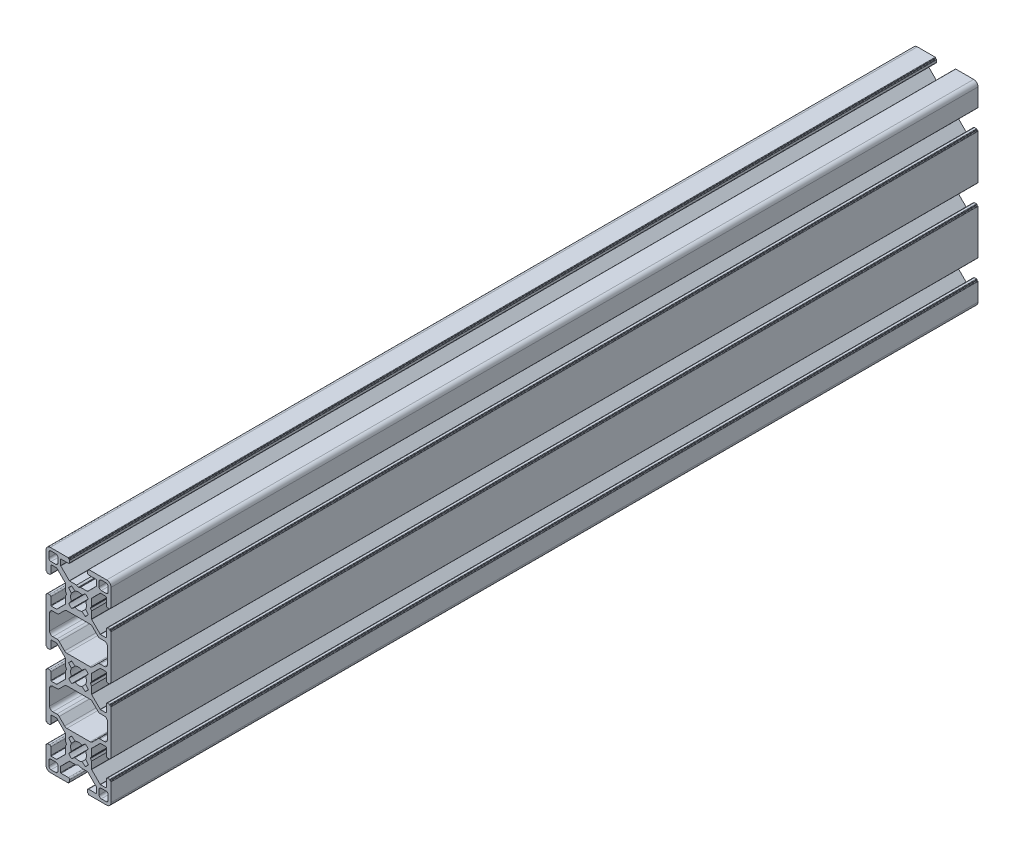
SolidWorks part; units mm, degrees
ref_plane "Спереди" through (0, 0, 0) normal (0, 0, 1) x (1, 0, 0)
ref_plane "Сверху" through (0, 0, 0) normal (0, 1, 0) x (1, 0, 0)
ref_plane "Справа" through (0, 0, 0) normal (1, 0, 0) x (0, 0, -1)
sketch "Эскиз1" plane through (0, 0, 0) normal (0, 0, 1) x (1, 0, 0)
  line L1 (6.0045, 46.509) -> (5.5426, 45.709)
  line L2 (1.6001, 12.3284) -> (3.1547, 11.1036)
  line L3 (4.1172, 9.609) -> (0.9, 9.609)
  line L4 (4.35, 1.109) -> (4.25, 1.109)
  line L5 (4.05, 1.309) -> (4.05, 2.209)
  line L6 (4.55, 0.909) -> (4.55, 0.809)
  line L7 (0.9, 9.609) -> (0.1019, 10.0697)
  line L8 (1.6001, 18.8895) -> (3.1547, 20.1143)
  line L9 (3.2806, 17.2091) -> (4.5184, 18.7449)
  line L10 (3.2806, 14.0088) -> (4.5184, 12.473)
  line L11 (6.0045, 11.4873) -> (6.0045, 14.709)
  line L12 (12.6, 7.359) -> (10.1328, 7.359)
  line L13 (10.5, 6.109) -> (12.7, 6.109)
  line L14 (12.7, 1.909) -> (10.5, 1.909)
  line L15 (15, 2.609) -> (15, 10.859)
  line L16 (13.7, 5.109) -> (13.7, 2.909)
  line L17 (14.8, 11.059) -> (14.7, 11.059)
  line L18 (14.5, 11.259) -> (14.5, 11.359)
  line L19 (14.3, 11.559) -> (13.4, 11.559)
  line L20 (12.8, 10.959) -> (12.8, 7.559)
  line L21 (8.25, 3.009) -> (8.25, 5.4761)
  line L22 (9.5, 2.909) -> (9.5, 5.109)
  line L23 (9.9914, 7.4175) -> (6.063, 11.3459)
  line L24 (12.8, 20.259) -> (12.8, 23.659)
  line L25 (15, 40.859) -> (15, 20.359)
  line L26 (9.9914, 23.8004) -> (6.063, 19.872)
  line L27 (8.9272, 25.0696) -> (6.4104, 22.5528)
  line L28 (14.3, 19.659) -> (13.4, 19.659)
  line L29 (14.5, 19.959) -> (14.5, 19.859)
  line L30 (14.8, 20.159) -> (14.7, 20.159)
  line L31 (6.0045, 19.7306) -> (6.0045, 16.509)
  line L32 (6.0045, 14.709) -> (5.5426, 15.509)
  line L33 (6.0045, 16.509) -> (5.5426, 15.709)
  line L34 (12.6, 23.859) -> (10.1328, 23.859)
  line L35 (11.85, 25.509) -> (9.9879, 25.509)
  line L36 (13.35, 34.209) -> (13.35, 27.009)
  line L37 (4.75, 0.609) -> (13, 0.609)
  line L38 (8.1914, 5.6175) -> (4.2586, 9.5504)
  line L39 (4.65, 2.809) -> (8.05, 2.809)
  line L46 (-1.6001, 42.3284) -> (-3.1547, 41.1036)
  line L47 (-5.3497, 39.1045) -> (5.3497, 39.1045)
  line L48 (-3.2806, 44.0088) -> (-4.5184, 42.473)
  line L63 (-12.8, 40.959) -> (-12.8, 37.559)
  line L64 (-9.9914, 37.4175) -> (-6.063, 41.3459)
  line L65 (-8.9272, 36.1483) -> (-6.4104, 38.6652)
  line L66 (-14.3, 41.559) -> (-13.4, 41.559)
  line L67 (-14.5, 41.259) -> (-14.5, 41.359)
  line L68 (-14.8, 41.059) -> (-14.7, 41.059)
  line L69 (-6.0045, 41.4873) -> (-6.0045, 44.709)
  line L71 (-6.0045, 44.709) -> (-5.5426, 45.509)
  line L72 (-12.6, 37.359) -> (-10.1328, 37.359)
  line L73 (-11.85, 35.709) -> (-9.9879, 35.709)
  line L80 (11.85, 35.709) -> (9.9879, 35.709)
  line L81 (12.6, 37.359) -> (10.1328, 37.359)
  line L82 (6.0045, 44.709) -> (5.5426, 45.509)
  line L84 (6.0045, 41.4873) -> (6.0045, 44.709)
  line L85 (14.8, 41.059) -> (14.7, 41.059)
  line L86 (14.5, 41.259) -> (14.5, 41.359)
  line L87 (14.3, 41.559) -> (13.4, 41.559)
  line L88 (8.9272, 36.1483) -> (6.4104, 38.6652)
  line L89 (9.9914, 37.4175) -> (6.063, 41.3459)
  line L90 (12.8, 40.959) -> (12.8, 37.559)
  line L105 (3.2806, 44.0088) -> (4.5184, 42.473)
  line L106 (1.6001, 42.3284) -> (3.1547, 41.1036)
  line L146 (-6.0045, 46.509) -> (-5.5426, 45.709)
  line L147 (-6.0045, 49.7306) -> (-6.0045, 46.509)
  line L150 (-1.6001, 48.8895) -> (-3.1547, 50.1143)
  line L155 (-3.2806, 47.2091) -> (-4.5184, 48.7449)
  line L156 (-4.65, 2.809) -> (-8.05, 2.809)
  line L157 (-8.1914, 5.6175) -> (-4.2586, 9.5504)
  line L158 (-4.75, 0.609) -> (-13, 0.609)
  line L162 (-13.35, 34.209) -> (-13.35, 27.009)
  line L163 (-11.85, 25.509) -> (-9.9879, 25.509)
  line L164 (-12.6, 23.859) -> (-10.1328, 23.859)
  line L165 (-6.0045, 16.509) -> (-5.5426, 15.709)
  line L166 (-6.0045, 14.709) -> (-5.5426, 15.509)
  line L167 (-6.0045, 19.7306) -> (-6.0045, 16.509)
  line L168 (-14.8, 20.159) -> (-14.7, 20.159)
  line L169 (-14.5, 19.959) -> (-14.5, 19.859)
  line L170 (-14.3, 19.659) -> (-13.4, 19.659)
  line L171 (-8.9272, 25.0696) -> (-6.4104, 22.5528)
  line L172 (-9.9914, 23.8004) -> (-6.063, 19.872)
  line L173 (-15, 40.859) -> (-15, 20.359)
  line L174 (-12.8, 20.259) -> (-12.8, 23.659)
  line L176 (-9.9914, 7.4175) -> (-6.063, 11.3459)
  line L177 (-9.5, 2.909) -> (-9.5, 5.109)
  line L178 (-8.25, 3.009) -> (-8.25, 5.4761)
  line L179 (-12.8, 10.959) -> (-12.8, 7.559)
  line L180 (-14.3, 11.559) -> (-13.4, 11.559)
  line L181 (-14.5, 11.259) -> (-14.5, 11.359)
  line L182 (-14.8, 11.059) -> (-14.7, 11.059)
  line L183 (-13.7, 5.109) -> (-13.7, 2.909)
  line L184 (-15, 2.609) -> (-15, 10.859)
  line L185 (-12.7, 1.909) -> (-10.5, 1.909)
  line L186 (-10.5, 6.109) -> (-12.7, 6.109)
  line L187 (-12.6, 7.359) -> (-10.1328, 7.359)
  line L188 (-6.0045, 11.4873) -> (-6.0045, 14.709)
  line L198 (1.6001, 48.8895) -> (3.1547, 50.1143)
  line L199 (-14.8, 50.159) -> (-14.7, 50.159)
  line L200 (-14.5, 49.959) -> (-14.5, 49.859)
  line L201 (-14.3, 49.659) -> (-13.4, 49.659)
  line L202 (3.2806, 47.2091) -> (4.5184, 48.7449)
  line L203 (14.3, 49.659) -> (13.4, 49.659)
  line L204 (14.5, 49.959) -> (14.5, 49.859)
  line L205 (14.8, 50.159) -> (14.7, 50.159)
  line L206 (6.0045, 49.7306) -> (6.0045, 46.509)
  line L207 (-5.3497, 52.1134) -> (5.3497, 52.1134)
  line L208 (-1.6001, 78.8895) -> (-3.1547, 80.1143)
  line L209 (-4.1172, 81.609) -> (-0.9, 81.609)
  line L210 (-4.35, 90.109) -> (-4.25, 90.109)
  line L211 (-4.05, 89.909) -> (-4.05, 89.009)
  line L212 (-4.55, 90.309) -> (-4.55, 90.409)
  line L213 (-0.9, 81.609) -> (-0.1019, 81.1482)
  line L214 (-3.2806, 14.0088) -> (-4.5184, 12.473)
  line L215 (-3.2806, 17.2091) -> (-4.5184, 18.7449)
  line L216 (-5.3497, 22.1134) -> (5.3497, 22.1134)
  line L217 (-1.6001, 18.8895) -> (-3.1547, 20.1143)
  line L218 (-1.6001, 72.3284) -> (-3.1547, 71.1036)
  line L219 (-5.3497, 69.1045) -> (5.3497, 69.1045)
  line L220 (-3.2806, 74.0088) -> (-4.5184, 72.473)
  line L221 (-3.2806, 77.2091) -> (-4.5184, 78.7449)
  line L222 (-6.0045, 79.7306) -> (-6.0045, 76.509)
  line L223 (-12.6, 83.859) -> (-10.1328, 83.859)
  line L224 (-10.5, 85.109) -> (-12.7, 85.109)
  line L225 (-12.7, 89.309) -> (-10.5, 89.309)
  line L226 (-0.9, 9.609) -> (-0.1019, 10.0697)
  line L227 (-15, 88.609) -> (-15, 80.359)
  line L228 (-13.7, 86.109) -> (-13.7, 88.309)
  line L229 (-14.8, 80.159) -> (-14.7, 80.159)
  line L230 (-14.5, 79.959) -> (-14.5, 79.859)
  line L231 (-14.3, 79.659) -> (-13.4, 79.659)
  line L232 (-12.8, 80.259) -> (-12.8, 83.659)
  line L233 (-8.25, 88.209) -> (-8.25, 85.7418)
  line L234 (-4.55, 0.909) -> (-4.55, 0.809)
  line L235 (-4.05, 1.309) -> (-4.05, 2.209)
  line L236 (-4.35, 1.109) -> (-4.25, 1.109)
  line L237 (-4.1172, 9.609) -> (-0.9, 9.609)
  line L238 (-1.6001, 12.3284) -> (-3.1547, 11.1036)
  line L239 (-9.5, 88.309) -> (-9.5, 86.109)
  line L240 (-9.9914, 83.8004) -> (-6.063, 79.872)
  line L241 (-12.8, 70.959) -> (-12.8, 67.559)
  line L242 (-15, 50.359) -> (-15, 70.859)
  line L243 (-9.9914, 67.4175) -> (-6.063, 71.3459)
  line L244 (-8.9272, 66.1483) -> (-6.4104, 68.6652)
  line L245 (-14.3, 71.559) -> (-13.4, 71.559)
  line L246 (-14.5, 71.259) -> (-14.5, 71.359)
  line L247 (-14.8, 71.059) -> (-14.7, 71.059)
  line L248 (-6.0045, 71.4873) -> (-6.0045, 74.709)
  line L249 (-6.0045, 76.509) -> (-5.5426, 75.709)
  line L250 (-6.0045, 74.709) -> (-5.5426, 75.509)
  line L251 (-12.6, 67.359) -> (-10.1328, 67.359)
  line L252 (-11.85, 65.709) -> (-9.9879, 65.709)
  line L253 (-13.35, 57.009) -> (-13.35, 64.209)
  line L254 (-4.75, 90.609) -> (-13, 90.609)
  line L255 (-8.1914, 85.6004) -> (-4.2586, 81.6675)
  line L256 (-4.65, 88.409) -> (-8.05, 88.409)
  line L257 (12.8, 50.259) -> (12.8, 53.659)
  line L258 (9.9914, 53.8004) -> (6.063, 49.872)
  line L259 (8.9272, 55.0696) -> (6.4104, 52.5528)
  line L260 (12.6, 53.859) -> (10.1328, 53.859)
  line L261 (11.85, 55.509) -> (9.9879, 55.509)
  line L262 (-11.85, 55.509) -> (-9.9879, 55.509)
  line L263 (-12.6, 53.859) -> (-10.1328, 53.859)
  line L264 (-8.9272, 55.0696) -> (-6.4104, 52.5528)
  line L265 (-9.9914, 53.8004) -> (-6.063, 49.872)
  line L266 (-12.8, 50.259) -> (-12.8, 53.659)
  line L267 (4.65, 88.409) -> (8.05, 88.409)
  line L268 (8.1914, 85.6004) -> (4.2586, 81.6675)
  line L269 (4.75, 90.609) -> (13, 90.609)
  line L270 (13.35, 57.009) -> (13.35, 64.209)
  line L271 (11.85, 65.709) -> (9.9879, 65.709)
  line L272 (12.6, 67.359) -> (10.1328, 67.359)
  line L273 (6.0045, 74.709) -> (5.5426, 75.509)
  line L274 (6.0045, 76.509) -> (5.5426, 75.709)
  line L275 (6.0045, 71.4873) -> (6.0045, 74.709)
  line L276 (14.8, 71.059) -> (14.7, 71.059)
  line L277 (14.5, 71.259) -> (14.5, 71.359)
  line L278 (14.3, 71.559) -> (13.4, 71.559)
  line L279 (8.9272, 66.1483) -> (6.4104, 68.6652)
  line L280 (9.9914, 67.4175) -> (6.063, 71.3459)
  line L281 (15, 50.359) -> (15, 70.859)
  line L282 (12.8, 70.959) -> (12.8, 67.559)
  line L283 (9.9914, 83.8004) -> (6.063, 79.872)
  line L284 (9.5, 88.309) -> (9.5, 86.109)
  line L285 (8.25, 88.209) -> (8.25, 85.7418)
  line L286 (12.8, 80.259) -> (12.8, 83.659)
  line L287 (14.3, 79.659) -> (13.4, 79.659)
  line L288 (14.5, 79.959) -> (14.5, 79.859)
  line L289 (14.8, 80.159) -> (14.7, 80.159)
  line L290 (13.7, 86.109) -> (13.7, 88.309)
  line L291 (15, 88.609) -> (15, 80.359)
  line L292 (12.7, 89.309) -> (10.5, 89.309)
  line L293 (10.5, 85.109) -> (12.7, 85.109)
  line L294 (12.6, 83.859) -> (10.1328, 83.859)
  line L295 (6.0045, 79.7306) -> (6.0045, 76.509)
  line L296 (3.2806, 77.2091) -> (4.5184, 78.7449)
  line L297 (3.2806, 74.0088) -> (4.5184, 72.473)
  line L298 (1.6001, 72.3284) -> (3.1547, 71.1036)
  line L299 (0.9, 81.609) -> (0.1019, 81.1482)
  line L300 (4.55, 90.309) -> (4.55, 90.409)
  line L301 (4.05, 89.909) -> (4.05, 89.009)
  line L302 (4.35, 90.109) -> (4.25, 90.109)
  line L303 (4.1172, 81.609) -> (0.9, 81.609)
  line L304 (1.6001, 78.8895) -> (3.1547, 80.1143)
  arc A0 (4.5184, 12.473) -> (3.1547, 11.1036) centre (0, 15.609) cw
  arc A1 (4.35, 1.109) -> (4.55, 0.909) centre (4.35, 0.909) cw
  arc A2 (4.25, 1.109) -> (4.05, 1.309) centre (4.25, 1.309) cw
  arc A3 (4.75, 0.609) -> (4.55, 0.809) centre (4.75, 0.809) cw
  arc A4 (4.05, 2.209) -> (4.65, 2.809) centre (4.65, 2.209) cw
  arc A5 (4.1172, 9.609) -> (4.2586, 9.5504) centre (4.1172, 9.409) cw
  arc A6 (3.2806, 17.2091) -> (3.2806, 14.0088) centre (0, 15.609) cw
  arc A7 (3.1547, 20.1143) -> (4.5184, 18.7449) centre (0, 15.609) cw
  arc A8 (12.6, 23.859) -> (12.8, 23.659) centre (12.6, 23.659) cw
  arc A9 (13.35, 27.009) -> (11.85, 25.509) centre (11.85, 27.009) cw
  arc A10 (9.9914, 23.8004) -> (10.1328, 23.859) centre (10.1328, 23.659) cw
  arc A11 (8.9272, 25.0696) -> (9.9879, 25.509) centre (9.9879, 24.009) cw
  arc A12 (15, 2.609) -> (13, 0.609) centre (13, 2.609) cw
  arc A13 (12.7, 6.109) -> (13.7, 5.109) centre (12.7, 5.109) cw
  arc A14 (13.7, 2.909) -> (12.7, 1.909) centre (12.7, 2.909) cw
  arc A15 (14.7, 11.059) -> (14.5, 11.259) centre (14.7, 11.259) cw
  arc A16 (14.8, 11.059) -> (15, 10.859) centre (14.8, 10.859) cw
  arc A17 (14.3, 11.559) -> (14.5, 11.359) centre (14.3, 11.359) cw
  arc A18 (12.8, 10.959) -> (13.4, 11.559) centre (13.4, 10.959) cw
  arc A19 (12.8, 7.559) -> (12.6, 7.359) centre (12.6, 7.559) cw
  arc A20 (9.5, 5.109) -> (10.5, 6.109) centre (10.5, 5.109) cw
  arc A21 (8.1914, 5.6175) -> (8.25, 5.4761) centre (8.05, 5.4761) cw
  arc A22 (8.25, 3.009) -> (8.05, 2.809) centre (8.05, 3.009) cw
  arc A23 (10.5, 1.909) -> (9.5, 2.909) centre (10.5, 2.909) cw
  arc A24 (10.1328, 7.359) -> (9.9914, 7.4175) centre (10.1328, 7.559) cw
  arc A25 (6.063, 11.3459) -> (6.0045, 11.4873) centre (6.2045, 11.4873) cw
  arc A26 (14.5, 19.859) -> (14.3, 19.659) centre (14.3, 19.859) cw
  arc A27 (15, 20.359) -> (14.8, 20.159) centre (14.8, 20.359) cw
  arc A28 (14.5, 19.959) -> (14.7, 20.159) centre (14.7, 19.959) cw
  arc A29 (13.4, 19.659) -> (12.8, 20.259) centre (13.4, 20.259) cw
  arc A30 (5.5426, 15.509) -> (5.5426, 15.709) centre (5.7158, 15.609) cw
  arc A31 (6.0045, 19.7306) -> (6.063, 19.872) centre (6.2045, 19.7306) cw
  arc A32 (6.4104, 22.5528) -> (5.3497, 22.1134) centre (5.3497, 23.6134) cw
  arc A34 (1.6001, 42.3284) -> (-1.6001, 42.3284) centre (0, 45.609) cw
  arc A42 (-3.2806, 44.0088) -> (-3.2806, 47.2091) centre (0, 45.609) cw
  arc A43 (-3.1547, 41.1036) -> (-4.5184, 42.473) centre (0, 45.609) cw
  arc A44 (-12.6, 37.359) -> (-12.8, 37.559) centre (-12.6, 37.559) cw
  arc A45 (-13.35, 34.209) -> (-11.85, 35.709) centre (-11.85, 34.209) cw
  arc A46 (-9.9914, 37.4175) -> (-10.1328, 37.359) centre (-10.1328, 37.559) cw
  arc A47 (-8.9272, 36.1483) -> (-9.9879, 35.709) centre (-9.9879, 37.209) cw
  arc A62 (-14.5, 41.359) -> (-14.3, 41.559) centre (-14.3, 41.359) cw
  arc A63 (-15, 40.859) -> (-14.8, 41.059) centre (-14.8, 40.859) cw
  arc A64 (-14.5, 41.259) -> (-14.7, 41.059) centre (-14.7, 41.259) cw
  arc A65 (-13.4, 41.559) -> (-12.8, 40.959) centre (-13.4, 40.959) cw
  arc A66 (5.5426, 45.709) -> (5.5426, 45.509) centre (5.6426, 45.609) ccw
  arc A67 (-6.0045, 41.4873) -> (-6.063, 41.3459) centre (-6.2045, 41.4873) cw
  arc A68 (-6.4104, 38.6652) -> (-5.3497, 39.1045) centre (-5.3497, 37.6045) cw
  arc A69 (6.4104, 38.6652) -> (5.3497, 39.1045) centre (5.3497, 37.6045) ccw
  arc A70 (6.0045, 41.4873) -> (6.063, 41.3459) centre (6.2045, 41.4873) ccw
  arc A71 (-5.5426, 45.709) -> (-5.5426, 45.509) centre (-5.6426, 45.609) cw
  arc A72 (13.4, 41.559) -> (12.8, 40.959) centre (13.4, 40.959) ccw
  arc A73 (14.5, 41.259) -> (14.7, 41.059) centre (14.7, 41.259) ccw
  arc A74 (15, 40.859) -> (14.8, 41.059) centre (14.8, 40.859) ccw
  arc A75 (14.5, 41.359) -> (14.3, 41.559) centre (14.3, 41.359) ccw
  arc A90 (8.9272, 36.1483) -> (9.9879, 35.709) centre (9.9879, 37.209) ccw
  arc A91 (9.9914, 37.4175) -> (10.1328, 37.359) centre (10.1328, 37.559) ccw
  arc A92 (13.35, 34.209) -> (11.85, 35.709) centre (11.85, 34.209) ccw
  arc A93 (12.6, 37.359) -> (12.8, 37.559) centre (12.6, 37.559) ccw
  arc A94 (3.1547, 41.1036) -> (4.5184, 42.473) centre (0, 45.609) ccw
  arc A132 (3.2806, 44.0088) -> (3.2806, 47.2091) centre (0, 45.609) ccw
  arc A133 (-3.1547, 50.1143) -> (-4.5184, 48.7449) centre (0, 45.609) ccw
  arc A138 (-6.4104, 22.5528) -> (-5.3497, 22.1134) centre (-5.3497, 23.6134) ccw
  arc A140 (-6.0045, 19.7306) -> (-6.063, 19.872) centre (-6.2045, 19.7306) ccw
  arc A141 (-5.5426, 15.509) -> (-5.5426, 15.709) centre (-5.7158, 15.609) ccw
  arc A142 (-13.4, 19.659) -> (-12.8, 20.259) centre (-13.4, 20.259) ccw
  arc A143 (-14.5, 19.959) -> (-14.7, 20.159) centre (-14.7, 19.959) ccw
  arc A144 (-15, 20.359) -> (-14.8, 20.159) centre (-14.8, 20.359) ccw
  arc A145 (-14.5, 19.859) -> (-14.3, 19.659) centre (-14.3, 19.859) ccw
  arc A147 (-6.063, 11.3459) -> (-6.0045, 11.4873) centre (-6.2045, 11.4873) ccw
  arc A148 (-10.1328, 7.359) -> (-9.9914, 7.4175) centre (-10.1328, 7.559) ccw
  arc A149 (-10.5, 1.909) -> (-9.5, 2.909) centre (-10.5, 2.909) ccw
  arc A150 (-8.25, 3.009) -> (-8.05, 2.809) centre (-8.05, 3.009) ccw
  arc A151 (-8.1914, 5.6175) -> (-8.25, 5.4761) centre (-8.05, 5.4761) ccw
  arc A152 (-9.5, 5.109) -> (-10.5, 6.109) centre (-10.5, 5.109) ccw
  arc A153 (-12.8, 7.559) -> (-12.6, 7.359) centre (-12.6, 7.559) ccw
  arc A154 (-12.8, 10.959) -> (-13.4, 11.559) centre (-13.4, 10.959) ccw
  arc A155 (-14.3, 11.559) -> (-14.5, 11.359) centre (-14.3, 11.359) ccw
  arc A156 (-14.8, 11.059) -> (-15, 10.859) centre (-14.8, 10.859) ccw
  arc A157 (-14.7, 11.059) -> (-14.5, 11.259) centre (-14.7, 11.259) ccw
  arc A158 (-13.7, 2.909) -> (-12.7, 1.909) centre (-12.7, 2.909) ccw
  arc A159 (-12.7, 6.109) -> (-13.7, 5.109) centre (-12.7, 5.109) ccw
  arc A160 (-15, 2.609) -> (-13, 0.609) centre (-13, 2.609) ccw
  arc A173 (1.6001, 48.8895) -> (-1.6001, 48.8895) centre (0, 45.609) ccw
  arc A174 (-6.4104, 52.5528) -> (-5.3497, 52.1134) centre (-5.3497, 53.6134) ccw
  arc A177 (-13.4, 49.659) -> (-12.8, 50.259) centre (-13.4, 50.259) ccw
  arc A178 (-14.5, 49.959) -> (-14.7, 50.159) centre (-14.7, 49.959) ccw
  arc A179 (-15, 50.359) -> (-14.8, 50.159) centre (-14.8, 50.359) ccw
  arc A180 (-14.5, 49.859) -> (-14.3, 49.659) centre (-14.3, 49.859) ccw
  arc A181 (3.1547, 50.1143) -> (4.5184, 48.7449) centre (0, 45.609) cw
  arc A182 (14.5, 49.859) -> (14.3, 49.659) centre (14.3, 49.859) cw
  arc A183 (15, 50.359) -> (14.8, 50.159) centre (14.8, 50.359) cw
  arc A184 (-8.9272, 25.0696) -> (-9.9879, 25.509) centre (-9.9879, 24.009) ccw
  arc A185 (-9.9914, 23.8004) -> (-10.1328, 23.859) centre (-10.1328, 23.659) ccw
  arc A186 (-13.35, 27.009) -> (-11.85, 25.509) centre (-11.85, 27.009) ccw
  arc A187 (-12.6, 23.859) -> (-12.8, 23.659) centre (-12.6, 23.659) ccw
  arc A188 (-3.1547, 20.1143) -> (-4.5184, 18.7449) centre (0, 15.609) ccw
  arc A189 (-3.2806, 17.2091) -> (-3.2806, 14.0088) centre (0, 15.609) ccw
  arc A190 (14.5, 49.959) -> (14.7, 50.159) centre (14.7, 49.959) cw
  arc A191 (13.4, 49.659) -> (12.8, 50.259) centre (13.4, 50.259) cw
  arc A192 (6.0045, 49.7306) -> (6.063, 49.872) centre (6.2045, 49.7306) cw
  arc A193 (6.4104, 52.5528) -> (5.3497, 52.1134) centre (5.3497, 53.6134) cw
  arc A194 (-1.6001, 78.8895) -> (1.6001, 78.8895) centre (0, 75.609) cw
  arc A195 (1.6001, 72.3284) -> (-1.6001, 72.3284) centre (0, 75.609) cw
  arc A196 (-4.5184, 78.7449) -> (-3.1547, 80.1143) centre (0, 75.609) cw
  arc A197 (-4.35, 90.109) -> (-4.55, 90.309) centre (-4.35, 90.309) cw
  arc A198 (0.1019, 10.0697) -> (-0.1019, 10.0697) centre (0, 9.8932) ccw
  arc A199 (-4.25, 90.109) -> (-4.05, 89.909) centre (-4.25, 89.909) cw
  arc A200 (-4.75, 90.609) -> (-4.55, 90.409) centre (-4.75, 90.409) cw
  arc A201 (-4.05, 89.009) -> (-4.65, 88.409) centre (-4.65, 89.009) cw
  arc A202 (-4.1172, 81.609) -> (-4.2586, 81.6675) centre (-4.1172, 81.809) cw
  arc A203 (-4.1172, 9.609) -> (-4.2586, 9.5504) centre (-4.1172, 9.409) ccw
  arc A204 (-4.05, 2.209) -> (-4.65, 2.809) centre (-4.65, 2.209) ccw
  arc A205 (-4.75, 0.609) -> (-4.55, 0.809) centre (-4.75, 0.809) ccw
  arc A206 (-4.25, 1.109) -> (-4.05, 1.309) centre (-4.25, 1.309) ccw
  arc A207 (-4.35, 1.109) -> (-4.55, 0.909) centre (-4.35, 0.909) ccw
  arc A208 (-4.5184, 12.473) -> (-3.1547, 11.1036) centre (0, 15.609) ccw
  arc A209 (0.1019, 81.1482) -> (-0.1019, 81.1482) centre (0, 81.3248) cw
  arc A210 (-3.2806, 74.0088) -> (-3.2806, 77.2091) centre (0, 75.609) cw
  arc A211 (-3.1547, 71.1036) -> (-4.5184, 72.473) centre (0, 75.609) cw
  arc A212 (-12.6, 67.359) -> (-12.8, 67.559) centre (-12.6, 67.559) cw
  arc A213 (-13.35, 64.209) -> (-11.85, 65.709) centre (-11.85, 64.209) cw
  arc A214 (-9.9914, 67.4175) -> (-10.1328, 67.359) centre (-10.1328, 67.559) cw
  arc A215 (-8.9272, 66.1483) -> (-9.9879, 65.709) centre (-9.9879, 67.209) cw
  arc A216 (-15, 88.609) -> (-13, 90.609) centre (-13, 88.609) cw
  arc A217 (-12.7, 85.109) -> (-13.7, 86.109) centre (-12.7, 86.109) cw
  arc A218 (-13.7, 88.309) -> (-12.7, 89.309) centre (-12.7, 88.309) cw
  arc A219 (-14.7, 80.159) -> (-14.5, 79.959) centre (-14.7, 79.959) cw
  arc A220 (-14.8, 80.159) -> (-15, 80.359) centre (-14.8, 80.359) cw
  arc A221 (-14.3, 79.659) -> (-14.5, 79.859) centre (-14.3, 79.859) cw
  arc A222 (-12.8, 80.259) -> (-13.4, 79.659) centre (-13.4, 80.259) cw
  arc A223 (-12.8, 83.659) -> (-12.6, 83.859) centre (-12.6, 83.659) cw
  arc A224 (-9.5, 86.109) -> (-10.5, 85.109) centre (-10.5, 86.109) cw
  arc A225 (-8.1914, 85.6004) -> (-8.25, 85.7418) centre (-8.05, 85.7418) cw
  arc A226 (-8.25, 88.209) -> (-8.05, 88.409) centre (-8.05, 88.209) cw
  arc A227 (-10.5, 89.309) -> (-9.5, 88.309) centre (-10.5, 88.309) cw
  arc A228 (-10.1328, 83.859) -> (-9.9914, 83.8004) centre (-10.1328, 83.659) cw
  arc A229 (-6.063, 79.872) -> (-6.0045, 79.7306) centre (-6.2045, 79.7306) cw
  arc A230 (-14.5, 71.359) -> (-14.3, 71.559) centre (-14.3, 71.359) cw
  arc A231 (-15, 70.859) -> (-14.8, 71.059) centre (-14.8, 70.859) cw
  arc A232 (-14.5, 71.259) -> (-14.7, 71.059) centre (-14.7, 71.259) cw
  arc A233 (-13.4, 71.559) -> (-12.8, 70.959) centre (-13.4, 70.959) cw
  arc A234 (-5.5426, 75.709) -> (-5.5426, 75.509) centre (-5.7158, 75.609) cw
  arc A235 (-6.0045, 71.4873) -> (-6.063, 71.3459) centre (-6.2045, 71.4873) cw
  arc A236 (-6.4104, 68.6652) -> (-5.3497, 69.1045) centre (-5.3497, 67.6045) cw
  arc A237 (12.6, 53.859) -> (12.8, 53.659) centre (12.6, 53.659) cw
  arc A238 (13.35, 57.009) -> (11.85, 55.509) centre (11.85, 57.009) cw
  arc A239 (9.9914, 53.8004) -> (10.1328, 53.859) centre (10.1328, 53.659) cw
  arc A240 (8.9272, 55.0696) -> (9.9879, 55.509) centre (9.9879, 54.009) cw
  arc A241 (-8.9272, 55.0696) -> (-9.9879, 55.509) centre (-9.9879, 54.009) ccw
  arc A242 (-9.9914, 53.8004) -> (-10.1328, 53.859) centre (-10.1328, 53.659) ccw
  arc A243 (-13.35, 57.009) -> (-11.85, 55.509) centre (-11.85, 57.009) ccw
  arc A244 (-12.6, 53.859) -> (-12.8, 53.659) centre (-12.6, 53.659) ccw
  arc A245 (6.4104, 68.6652) -> (5.3497, 69.1045) centre (5.3497, 67.6045) ccw
  arc A246 (6.0045, 71.4873) -> (6.063, 71.3459) centre (6.2045, 71.4873) ccw
  arc A247 (5.5426, 75.709) -> (5.5426, 75.509) centre (5.7158, 75.609) ccw
  arc A248 (13.4, 71.559) -> (12.8, 70.959) centre (13.4, 70.959) ccw
  arc A249 (14.5, 71.259) -> (14.7, 71.059) centre (14.7, 71.259) ccw
  arc A250 (15, 70.859) -> (14.8, 71.059) centre (14.8, 70.859) ccw
  arc A251 (14.5, 71.359) -> (14.3, 71.559) centre (14.3, 71.359) ccw
  arc A252 (6.063, 79.872) -> (6.0045, 79.7306) centre (6.2045, 79.7306) ccw
  arc A253 (10.1328, 83.859) -> (9.9914, 83.8004) centre (10.1328, 83.659) ccw
  arc A254 (10.5, 89.309) -> (9.5, 88.309) centre (10.5, 88.309) ccw
  arc A255 (8.25, 88.209) -> (8.05, 88.409) centre (8.05, 88.209) ccw
  arc A256 (8.1914, 85.6004) -> (8.25, 85.7418) centre (8.05, 85.7418) ccw
  arc A257 (9.5, 86.109) -> (10.5, 85.109) centre (10.5, 86.109) ccw
  arc A258 (12.8, 83.659) -> (12.6, 83.859) centre (12.6, 83.659) ccw
  arc A259 (12.8, 80.259) -> (13.4, 79.659) centre (13.4, 80.259) ccw
  arc A260 (14.3, 79.659) -> (14.5, 79.859) centre (14.3, 79.859) ccw
  arc A261 (1.6001, 18.8895) -> (-1.6001, 18.8895) centre (0, 15.609) ccw
  arc A262 (14.8, 80.159) -> (15, 80.359) centre (14.8, 80.359) ccw
  arc A263 (-1.6001, 12.3284) -> (1.6001, 12.3284) centre (0, 15.609) ccw
  arc A264 (14.7, 80.159) -> (14.5, 79.959) centre (14.7, 79.959) ccw
  arc A265 (13.7, 88.309) -> (12.7, 89.309) centre (12.7, 88.309) ccw
  arc A266 (12.7, 85.109) -> (13.7, 86.109) centre (12.7, 86.109) ccw
  arc A267 (15, 88.609) -> (13, 90.609) centre (13, 88.609) ccw
  arc A268 (8.9272, 66.1483) -> (9.9879, 65.709) centre (9.9879, 67.209) ccw
  arc A269 (9.9914, 67.4175) -> (10.1328, 67.359) centre (10.1328, 67.559) ccw
  arc A270 (13.35, 64.209) -> (11.85, 65.709) centre (11.85, 64.209) ccw
  arc A271 (12.6, 67.359) -> (12.8, 67.559) centre (12.6, 67.559) ccw
  arc A272 (3.1547, 71.1036) -> (4.5184, 72.473) centre (0, 75.609) ccw
  arc A273 (3.2806, 74.0088) -> (3.2806, 77.2091) centre (0, 75.609) ccw
  arc A274 (4.1172, 81.609) -> (4.2586, 81.6675) centre (4.1172, 81.809) ccw
  arc A275 (4.05, 89.009) -> (4.65, 88.409) centre (4.65, 89.009) ccw
  arc A276 (4.75, 90.609) -> (4.55, 90.409) centre (4.75, 90.409) ccw
  arc A277 (4.25, 90.109) -> (4.05, 89.909) centre (4.25, 89.909) ccw
  arc A278 (4.35, 90.109) -> (4.55, 90.309) centre (4.35, 90.309) ccw
  arc A279 (4.5184, 78.7449) -> (3.1547, 80.1143) centre (0, 75.609) ccw
  arc A280 (-6.063, 49.872) -> (-6.0045, 49.7306) centre (-6.1045, 49.772) cw
  point P178 (0, 22.1134)
  point P382 (0, 39.1045)
  point P385 (-15, 30.609)
  point P387 (-13.35, 30.609)
  point P388 (13.35, 30.609)
  point P390 (15, 30.609)
  point P564 (15, 60.609)
  point P565 (13.35, 60.609)
  point P566 (-13.35, 60.609)
  point P567 (-15, 60.609)
  point P568 (0, 69.1045)
extrude "Бобышка-Вытянуть1" add sketch "Эскиз1" along normal blind 400
